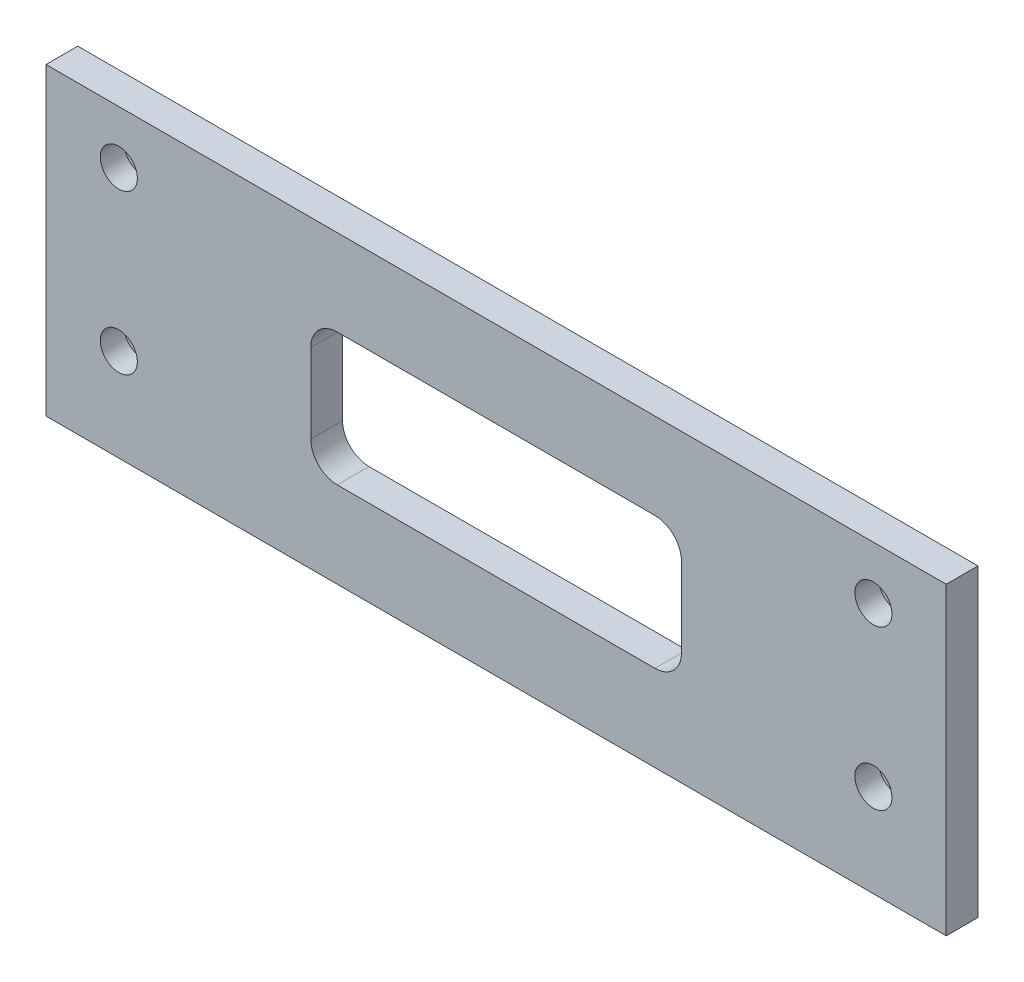
SolidWorks part; units mm, degrees
material "AISI 1035 钢 (SS)"
ref_plane "前视基准面" through (0, 0, 0) normal (0, 0, 1) x (1, 0, 0)
ref_plane "上视基准面" through (0, 0, 0) normal (0, 1, 0) x (1, 0, 0)
ref_plane "右视基准面" through (0, 0, 0) normal (1, 0, 0) x (0, 0, -1)
sketch "草图1" plane through (0, 0, 0) normal (0, 0, 1) x (1, 0, 0)
  line L1 (-170, -57.5) -> (170, -57.5)
  line L2 (-170, -57.5) -> (-170, 57.5)
  line L3 (-170, 57.5) -> (170, 57.5)
  line L4 (170, -57.5) -> (170, 57.5)
  line L5 (-170, -57.5) -> (170, 57.5) construction
  line L6 (-170, 57.5) -> (170, -57.5) construction
  point P0 (0, 0)
  dimension "D1" = 340
  dimension "D2" = 115
extrude "凸台-拉伸1" add sketch "草图1" along normal blind 12
hole_wizard "打孔尺寸(%根据)内六角圆柱头螺钉的类型1" positions "草图2" profile "草图3" counterbore size "M8" standard "GB" end condition through all
sketch "草图2" plane through (0, 0, 12) normal (0, 0, 1) x (1, 0, 0)
  line L3 (0, 64.6802) -> (0, -59.4413) construction
  line L4 (170, 57.5) -> (-170, 57.5) construction
  point P0 (-142.5, 37.5)
  point P14 (142.5, 37.5)
  point P15 (142.5, -22.5)
  point P16 (-142.5, -22.5)
  dimension "D1" = 60
  dimension "D2" = 285
  dimension "D3" = 20
  dimension "D4" = 60
sketch "草图3" plane through (-142.5, 37.5, 12) normal (1, 0, 0) x (0, -1, 0)
  line L0 (0, 0) -> (0, 12)
  line L1 (0, 12) -> (4.5, 12)
  line L3 (4.5, 12) -> (4.5, 9)
  line L4 (4.5, 9) -> (7, 9)
  line L5 (7, 9) -> (7, 0)
  line L7 (7, 0) -> (0, 0)
  line L11 (0, -6.35) -> (0, 107.95) construction
  dimension "通孔孔直径" = 9
  dimension "通孔孔深度" = 12
  dimension "柱形沉头孔直径" = 14
  dimension "柱形沉头孔深度" = 9
sketch "草图4" plane through (0, 0, 12) normal (0, 0, 1) x (1, 0, 0)
  line L0 (0, 57.5) -> (0, -57.5) construction
  line L1 (170, 57.5) -> (-170, 57.5) construction
  line L2 (-170, -57.5) -> (170, -57.5) construction
  line L4 (-60, 25) -> (60, 25)
  line L5 (-70, 15) -> (-70, -15)
  line L6 (-60, -25) -> (60, -25)
  line L7 (70, 15) -> (70, -15)
  line L8 (-70, 25) -> (70, -25) construction
  line L9 (-70, -25) -> (70, 25) construction
  arc A0 (60, -25) -> (70, -15) centre (60, -15) ccw
  arc A1 (60, 25) -> (70, 15) centre (60, 15) cw
  arc A2 (-70, -15) -> (-60, -25) centre (-60, -15) ccw
  arc A3 (-60, 25) -> (-70, 15) centre (-60, 15) ccw
  point P6 (0, 0)
  dimension "D3" = 10
  dimension "D1" = 50
  dimension "D2" = 140
extrude "切除-拉伸1" cut sketch "草图4" against normal through all
